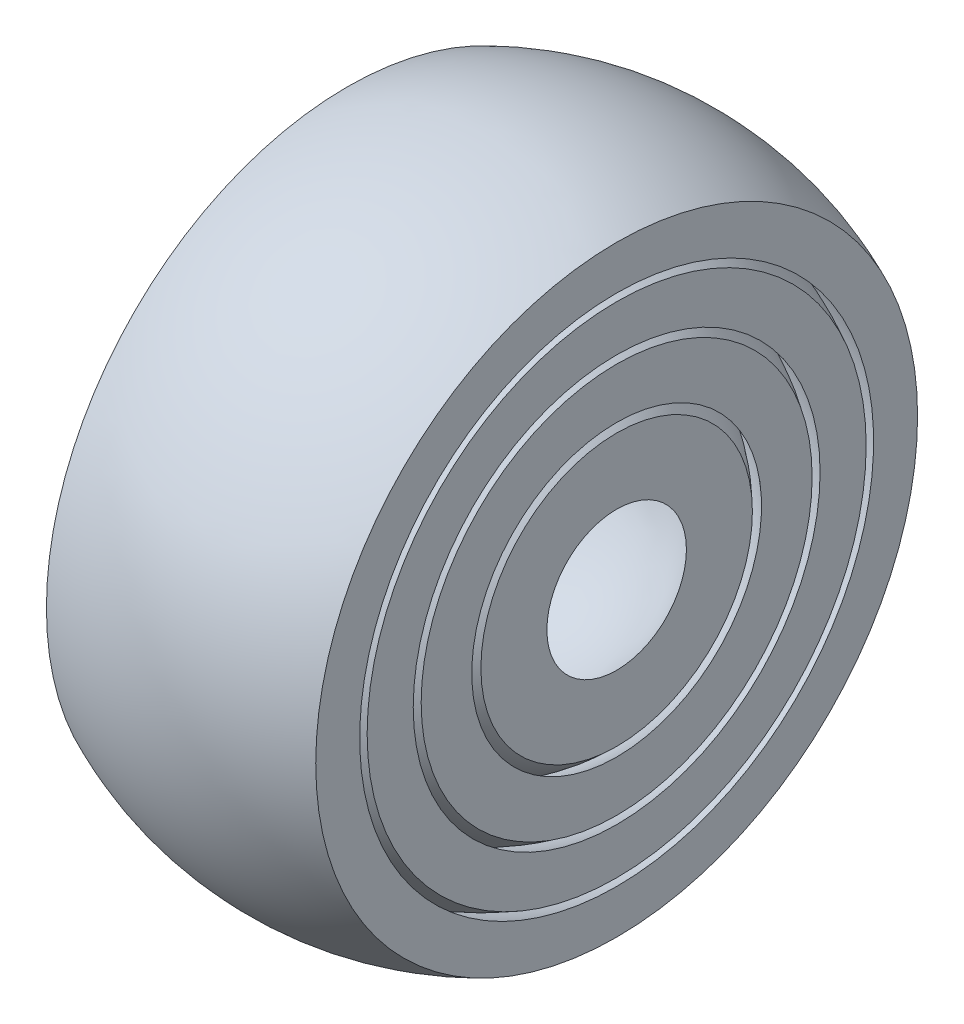
SolidWorks part; units mm, degrees
ref_plane "Alzado" through (0, 0, 0) normal (0, 0, 1) x (1, 0, 0)
ref_plane "Planta" through (0, 0, 0) normal (0, 1, 0) x (1, 0, 0)
ref_plane "Vista lateral" through (0, 0, 0) normal (1, 0, 0) x (0, 0, -1)
sketch "Sketch1" plane through (0, 0, 0) normal (0, 0, 1) x (1, 0, 0)
  line L0 (0, 60.1133) -> (0, -55.0063) construction
  line L1 (0, 50) -> (0, 44)
  line L2 (0, -44) -> (0, -50)
  line L3 (0, 43) -> (0, 37)
  line L4 (0, -37) -> (0, -43)
  line L5 (0, 36) -> (0, 30)
  line L6 (0, -30) -> (0, -36)
  line L7 (0, 29) -> (0, 23)
  line L8 (0, -23) -> (0, -29)
  arc A0 (0, 50) -> (0, -50) centre (0, 0) ccw
  arc A1 (0, 44) -> (0, -44) centre (0, 0) ccw
  arc A2 (0, 43) -> (0, -43) centre (0, 0) ccw
  arc A3 (0, 37) -> (0, -37) centre (0, 0) ccw
  arc A4 (0, 36) -> (0, -36) centre (0, 0) ccw
  arc A5 (0, 30) -> (0, -30) centre (0, 0) ccw
  arc A6 (0, 29) -> (0, -29) centre (0, 0) ccw
  arc A7 (0, 23) -> (0, -23) centre (0, 0) ccw
  dimension "D1" = 100
  dimension "D2" = 88
  dimension "D3" = 86
  dimension "D4" = 74
  dimension "D5" = 72
  dimension "D6" = 60
  dimension "D7" = 58
  dimension "D8" = 46
revolve "Revolve1" add sketch "Sketch1" angle 360 about L0
sketch "Sketch4" plane through (0, 0, 0) normal (0, 0, 1) x (1, 0, 0)
  line L0 (0, 60.1273) -> (0, -55.7291) construction
  line L1 (-64.0423, 65.1712) -> (-20.422, 65.1712)
  line L2 (-64.0423, 65.1712) -> (-64.0423, -55.7291)
  line L3 (-64.0423, -55.7291) -> (-20.422, -55.7291)
  line L4 (-20.422, 65.1712) -> (-20.422, -55.7291)
  line L5 (20.422, 65.1712) -> (20.422, -55.7291)
  line L6 (64.0423, -55.7291) -> (20.422, -55.7291)
  line L7 (64.0423, 65.1712) -> (64.0423, -55.7291)
  line L8 (64.0423, 65.1712) -> (20.422, 65.1712)
extrude "Cut-Extrude5" cut sketch "Sketch4" against normal through all and the other way through all
